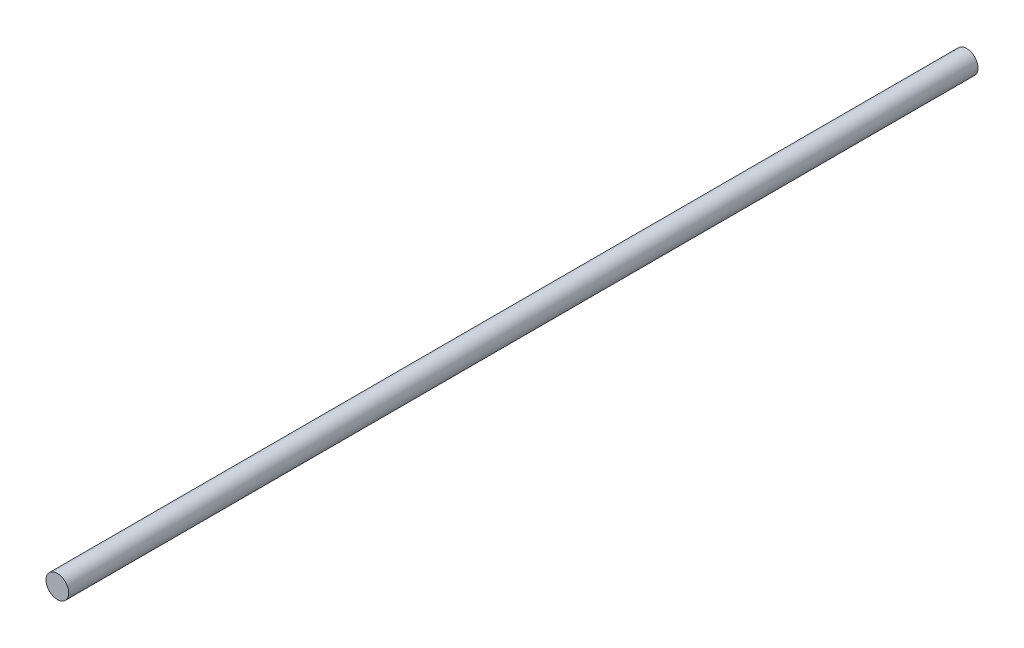
SolidWorks part; units mm, degrees
ref_plane "Alzado" through (0, 0, 0) normal (0, 0, 1) x (1, 0, 0)
ref_plane "Planta" through (0, 0, 0) normal (0, 1, 0) x (1, 0, 0)
ref_plane "Vista lateral" through (0, 0, 0) normal (1, 0, 0) x (0, 0, -1)
sketch "Croquis1" plane through (0, 0, 0) normal (0, 0, 1) x (1, 0, 0)
  circle A0 centre (0, 0) radius 2.5
  dimension "D1" = 5
extrude "Saliente-Extruir1" add sketch "Croquis1" along normal mid plane 200
